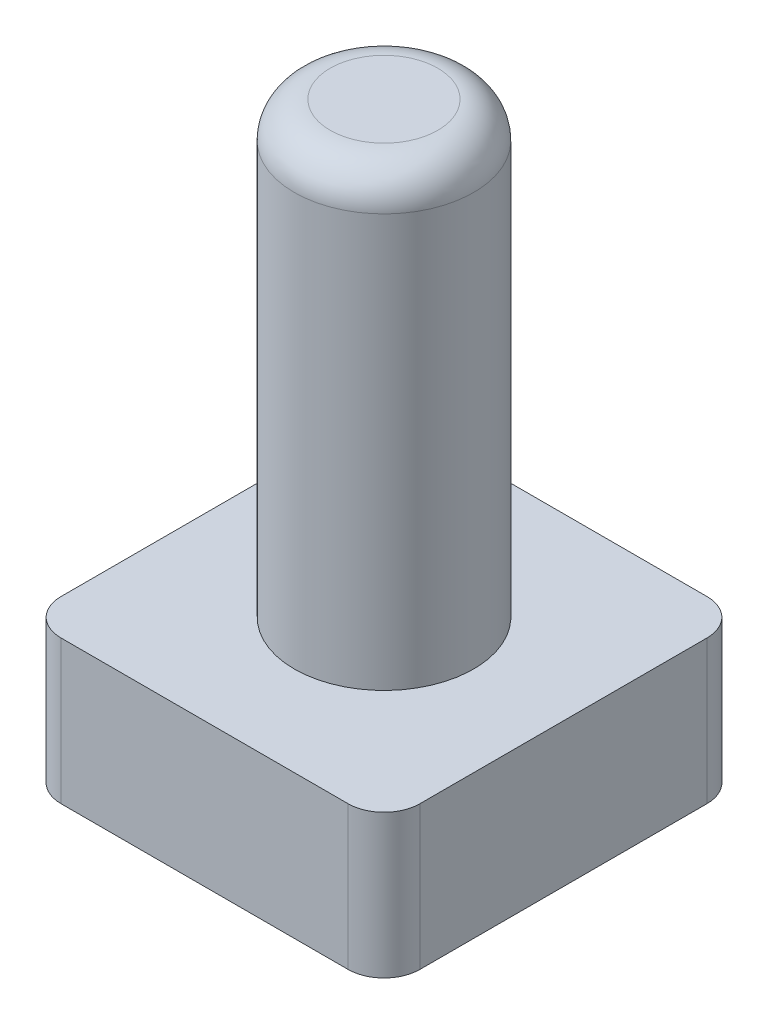
SolidWorks part; units mm, degrees
ref_plane "Front Plane" through (0, 0, 0) normal (0, 0, 1) x (1, 0, 0)
ref_plane "Top Plane" through (0, 0, 0) normal (0, 1, 0) x (1, 0, 0)
ref_plane "Right Plane" through (0, 0, 0) normal (1, 0, 0) x (0, 0, -1)
sketch "Sketch1" plane through (0, 0, 0) normal (0, 1, 0) x (1, 0, 0)
  line L0 (1.5, 8.5) -> (8.5, 8.5)
  line L1 (0, 0) -> (10, 0)
  line L2 (0, 0) -> (0, 10)
  line L3 (0, 10) -> (10, 10)
  line L4 (10, 0) -> (10, 10)
  line L5 (0, 0) -> (10, 10) construction
  line L6 (0, 10) -> (10, 0) construction
  line L7 (8.5, 1.5) -> (8.5, 8.5)
  line L8 (1.5, 1.5) -> (8.5, 1.5)
  line L9 (1.5, 1.5) -> (1.5, 8.5)
  point P4 (5, 5)
  dimension "D1" = 7
  dimension "D2" = 7
  dimension "D3" = 1.5
extrude "Boss-Extrude1" add sketch "Sketch1" along normal blind 3
sketch "Sketch2" plane through (0, 3, 0) normal (0, 1, 0) x (1, 0, 0)
  line L0 (10, 0) -> (10, 10) construction
  line L1 (10, 10) -> (0, 10) construction
  line L2 (0, 10) -> (0, 0) construction
  line L3 (0, 0) -> (10, 0) construction
  line L4 (10, 0) -> (10, 10)
  line L5 (10, 10) -> (0, 10)
  line L6 (0, 10) -> (0, 0)
  line L7 (0, 0) -> (10, 0)
extrude "Boss-Extrude2" add sketch "Sketch2" along normal blind 1
sketch "Sketch3" plane through (0, 4, 0) normal (0, 1, 0) x (1, 0, 0)
  line L0 (0, 10) -> (10, 0) construction
  line L1 (0, 0) -> (10, 10) construction
  circle A0 centre (5, 5) radius 2.5
  dimension "D1" = 5
extrude "Boss-Extrude3" add sketch "Sketch3" along normal blind 12.5
fillet "Fillet1" radius 1 5 edges at (5, 16.5, -2.5) (0, 2, -10) (10, 2, -10) (10, 2, 0) (0, 2, 0)
